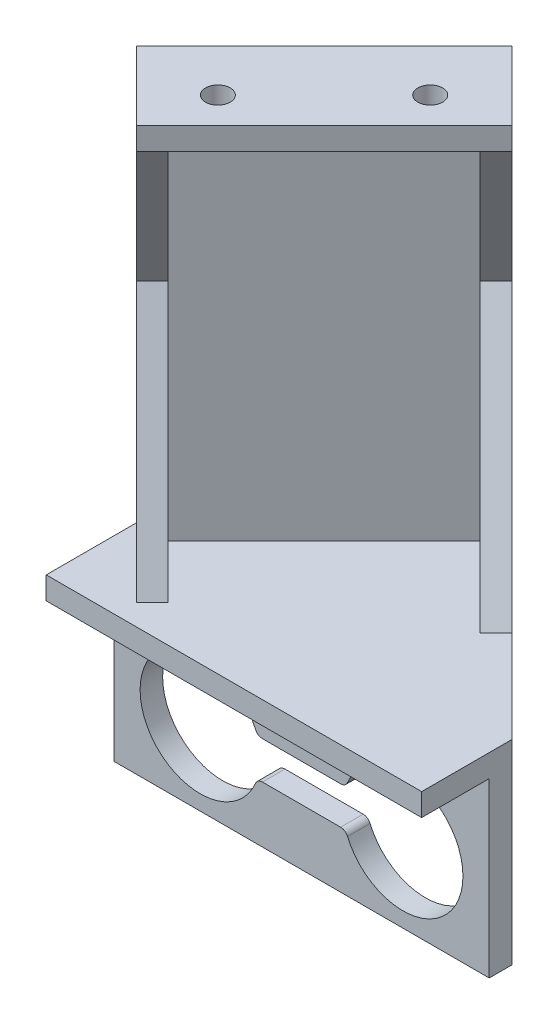
SolidWorks part; units mm, degrees
other "标注1"
sketch "草图6" plane through (25, -10, 15) normal (0.0929, -0.9273, 0.3626) x (0.5024, 0.3581, 0.787)
other "标注2"
sketch "草图7" plane through (25, -10, 15) normal (0.0929, -0.9273, 0.3626) x (0.5024, 0.3581, 0.787)
other "标注3"
sketch "草图8" plane through (25, -10, 15) normal (0.0929, -0.9273, 0.3626) x (0.5024, 0.3581, 0.787)
ref_plane "前视基准面" through (0, 0, 0) normal (0, 0, 1) x (1, 0, 0)
ref_plane "上视基准面" through (0, 0, 0) normal (0, 1, 0) x (1, 0, 0)
ref_plane "右视基准面" through (0, 0, 0) normal (1, 0, 0) x (0, 0, -1)
sketch "草图1" plane through (0, 0, 0) normal (0, 0, 1) x (1, 0, 0)
  line L1 (25, -10) -> (-25, -10)
  line L2 (25, -10) -> (25, 10)
  line L3 (25, 10) -> (-25, 10)
  line L4 (-25, -10) -> (-25, 10)
  line L5 (25, -10) -> (-25, 10) construction
  line L6 (25, 10) -> (-25, -10) construction
  line L8 (-5.2084, 2.5) -> (5.2084, 2.5)
  line L9 (5.2084, -2.5) -> (-5.2084, -2.5)
  line L10 (3.25, 7.25) -> (-3.25, 7.25) construction
  line L11 (3.25, 5.5) -> (-3.25, 5.5)
  line L12 (3.25, 9) -> (-3.25, 9)
  arc A7 (6.1297, -3.1111) -> (6.1297, 3.1111) centre (13.5, 0) ccw
  arc A8 (-6.1297, 3.1111) -> (-6.1297, -3.1111) centre (-13.5, 0) ccw
  arc A9 (5.2084, -2.5) -> (6.1297, -3.1111) centre (5.2084, -3.5) cw
  arc A10 (5.2084, 2.5) -> (6.1297, 3.1111) centre (5.2084, 3.5) ccw
  arc A11 (-5.2084, -2.5) -> (-6.1297, -3.1111) centre (-5.2084, -3.5) ccw
  arc A12 (-5.2084, 2.5) -> (-6.1297, 3.1111) centre (-5.2084, 3.5) cw
  arc A13 (3.25, 5.5) -> (3.25, 9) centre (3.25, 7.25) ccw
  arc A14 (-3.25, 9) -> (-3.25, 5.5) centre (-3.25, 7.25) ccw
  point P0 (0, 0)
  point P22 (0, 7.25)
  dimension "D3" = 1
  dimension "D4" = 8
  dimension "D5" = 8
  dimension "D6" = 2.5
  dimension "D8" = 13.5
  dimension "D9" = 13.5
  dimension "D12" = 1.75
  dimension "D1" = 20
  dimension "D2" = 50
  dimension "D7" = 2.5
  dimension "D10" = 7.25
  dimension "D11" = 6.5
  dimension "D13" = 3.25
extrude "凸台-拉伸1" add sketch "草图1" along normal blind 3
sketch "草图2" plane through (0, 10, 0) normal (0, 1, 0) x (1, 0, 0)
  line L1 (-25, 0) -> (25, 0)
  line L2 (-25, 0) -> (-25, -12)
  line L3 (-25, -12) -> (25, -12)
  line L4 (25, 0) -> (25, -12)
  dimension "D1" = 12
extrude "凸台-拉伸2" add sketch "草图2" along normal blind 6
sketch "草图5" plane through (0, 10, 0) normal (0, -1, 0) x (1, 0, 0)
  line L1 (25, 3) -> (-25, 3)
  line L2 (25, 3) -> (25, 12)
  line L3 (25, 12) -> (-25, 12)
  line L4 (-25, 3) -> (-25, 12)
extrude "切除-拉伸2" cut sketch "草图5" against normal blind 3
sketch "草图9" plane through (0, 16, 0) normal (0, 1, 0) x (1, 0, 0)
  line L0 (25, 0) -> (0, 25)
  line L1 (0, 25) -> (-25, 0)
  line L2 (25, 0) -> (-25, 0)
extrude "凸台-拉伸3" add sketch "草图9" against normal blind 3
sketch "草图11" plane through (0, 16, 0) normal (0, 1, 0) x (1, 0, 0)
  line L0 (0, 25) -> (2.1213, 22.8787)
  line L1 (25, 0) -> (0, 25) construction
  line L2 (2.1213, 22.8787) -> (-22.8787, -2.1213)
  line L3 (-25, 0) -> (-22.8787, -2.1213)
  line L9 (-25, 0) -> (-25, -12)
  line L10 (-25, -12) -> (25, -12)
  line L11 (25, -12) -> (25, 0)
  line L12 (25, 0) -> (0, 25)
  line L13 (0, 25) -> (-25, 0)
  line L18 (0, 25) -> (-25, 0)
  dimension "D1" = 0
extrude "凸台-拉伸4" add sketch "草图11" along normal blind 55 contours L18 L3 L2 L0
sketch "草图12" plane through (-10.3787, 0, -10.3787) normal (0.7071, 0, 0.7071) x (0.7071, 0, -0.7071)
  line L2 (-17.6777, 71) -> (-17.6777, 68)
  line L5 (14.6777, 68) -> (-17.6777, 68)
  line L6 (14.6777, 68) -> (14.6777, 71)
  line L7 (14.6777, 71) -> (-17.6777, 71)
extrude "凸台-拉伸6" add sketch "草图12" along normal blind 10
sketch "草图13" plane through (12.5, 0, -12.5) normal (0.7071, 0, -0.7071) x (-0.7071, 0, -0.7071)
  line L0 (17.6777, 71) -> (4.6777, 71)
  line L1 (17.6777, 71) -> (17.6777, 46)
  line L2 (17.6777, 13) -> (17.6777, 71) construction
  line L3 (4.6777, 71) -> (4.6777, 68)
  line L4 (17.6777, 46) -> (14.6777, 46)
  line L5 (14.6777, 71) -> (14.6777, 16) construction
  line L6 (14.6777, 46) -> (4.6777, 68)
  line L7 (14.6777, 16) -> (-0.3223, 16)
  line L8 (-17.6777, 16) -> (14.6777, 16) construction
  line L9 (14.6777, 16) -> (14.6777, 46)
  line L10 (14.6777, 46) -> (-0.3223, 16)
  line L11 (4.6777, 68) -> (4.6777, 71) construction
  line M6 (14.6777, 16) -> (-17.6777, 16)
  line M11 (14.6777, 71) -> (14.6777, 16)
  dimension "D1" = 15
  dimension "D2" = 30
  dimension "D3" = 13
extrude "凸台-拉伸7" add sketch "草图13" against normal blind 3 contours L10 M11 M6 | L6 L0 L3 M11
sketch "草图14" plane through (-12.5, 0, 12.5) normal (-0.7071, 0, 0.7071) x (0.7071, 0, 0.7071)
  line L0 (-14.6777, 16) -> (-4.6777, 16)
  line L1 (-14.6777, 16) -> (-14.6777, 46)
  line L2 (-14.6777, 68) -> (-14.6777, 16) construction
  line L3 (-4.6777, 16) -> (-14.6777, 46)
  line L4 (-14.6777, 46) -> (-4.6777, 68)
  line L5 (-4.6777, 68) -> (-14.6777, 68)
  line L6 (-14.6777, 68) -> (-14.6777, 46)
  line M2 (-14.6777, 16) -> (-14.6777, 68)
  line M3 (-14.6777, 68) -> (-4.6777, 68)
  dimension "D1" = 30
  dimension "D2" = 10
extrude "凸台-拉伸8" add sketch "草图14" against normal blind 3 contours L0 L3 M2 | L4 M2 M3
sketch "草图15" plane through (0, 68, 0) normal (0, -1, 0) x (1, 0, 0)
  line L0 (7.0711, -13.6863) -> (0, -20.7574) construction
  line L1 (3.5355, -17.2218) -> (0.2279, -13.9142)
  line L2 (-20.7574, 0) -> (-13.6863, 7.0711) construction
  line L3 (-17.2218, 3.5355) -> (-13.9142, 0.2279)
  line L4 (0, -25) -> (-25, 0) construction
  circle A0 centre (0.2279, -13.9142) radius 1.65
  circle A1 centre (-13.9142, 0.2279) radius 1.65
  dimension "D1" = 20
extrude "切除-拉伸3" cut sketch "草图15" against normal blind 3
move or copy body "实体-移动/复制1" [suppressed] bodies to move or copy 118
